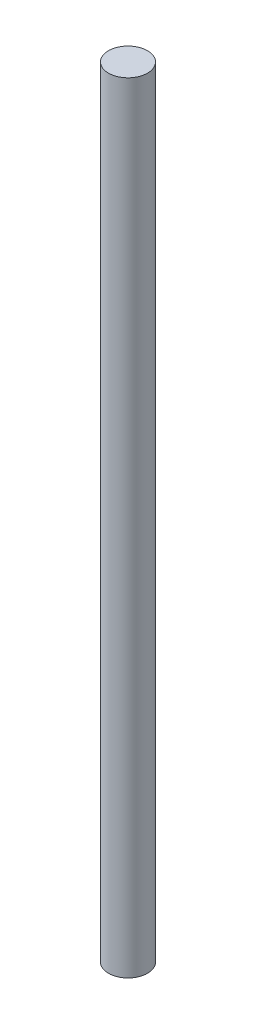
SolidWorks part; units mm, degrees
ref_plane "Front" through (0, 0, 0) normal (0, 0, 1) x (1, 0, 0)
ref_plane "Top" through (0, 0, 0) normal (0, 1, 0) x (1, 0, 0)
ref_plane "Right" through (0, 0, 0) normal (1, 0, 0) x (0, 0, -1)
sketch "Sketch1" plane through (0, 0, 0) normal (0, 1, 0) x (1, 0, 0)
  circle A0 centre (0, 0) radius 1.5
  dimension "D1" = 3
extrude "Boss-Extrude1" add sketch "Sketch1" along normal blind 60
